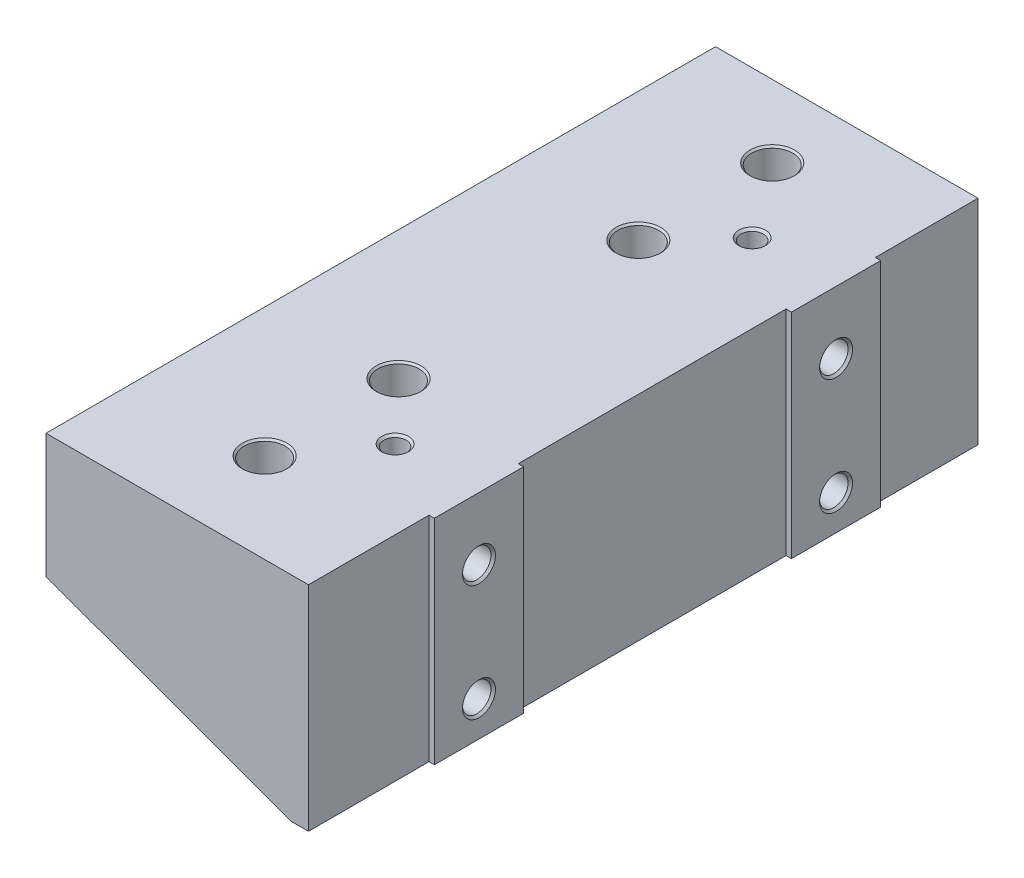
SolidWorks part; units mm, degrees
material "6061-T6 Al"
ref_plane "Front" through (0, 0, 0) normal (0, 0, 1) x (1, 0, 0)
ref_plane "Top" through (0, 0, 0) normal (0, 1, 0) x (1, 0, 0)
ref_plane "Right" through (0, 0, 0) normal (1, 0, 0) x (0, 0, -1)
sketch "Sketch13" plane through (0, 0, 0) normal (0, 0, 1) x (1, 0, 0)
  line L0 (0, -60.7572) -> (-6.35, -60.7572)
  line L8 (-76.2, -35.3339) -> (-6.35, -60.7572)
  line L9 (0, -60.7572) -> (0, 0)
  line L10 (0, 0) -> (-76.2, 0)
  line L11 (-76.2, 0) -> (-76.2, -35.3339)
  dimension "D1" = 76.2
  dimension "D2" = 6.35
  dimension "D3" = 70
  dimension "D4" = 60.7572
extrude "Extrude1" add sketch "Sketch13" along normal mid plane 190.5
hole_wizard "Tapped Hole for 3/8-16 Helicoil1" positions "Sketch15" profile "Sketch14" tap size "3/8-16" standard "Helicoil® Inch" end condition through all
sketch "Sketch15" plane through (0, 0, 0) normal (0, 1, 0) x (-1, 0, 0)
  point P0 (39.497, 69.7484)
  point P3 (39.497, 31.6484)
  point P6 (39.497, -36.576)
  point P9 (39.497, -74.676)
  dimension "D1" = 31.6484
  dimension "D2" = 38.1
  dimension "D3" = 38.1
  dimension "D4" = 74.676
  dimension "D5" = 39.497
sketch "Sketch14" plane through (-39.497, 0, 69.7484) normal (1, 0, 0) x (0, 0, 1)
  line L0 (0, 0) -> (0, 60.7572)
  line L1 (0, 60.7572) -> (5.0419, 60.7572)
  line L3 (5.0419, 60.7572) -> (5.0419, 28.702)
  line L4 (5.8445, 28.702) -> (5.0419, 28.702)
  line L5 (5.8445, 28.702) -> (5.8445, 0.5055)
  line L6 (5.8445, 0.5055) -> (6.35, 0)
  line L7 (6.35, 0) -> (0, 0)
  line L8 (-5.8445, 0.5055) -> (-6.35, 0) construction
  line L11 (0, -6.35) -> (0, 107.95) construction
  dimension "Thru Tap Drill Dia." = 10.0838
  dimension "Thru Tap Drill Depth" = 60.7572
  dimension "Thread Major Dia." = 11.6891
  dimension "Thread Depth" = 28.702
  dimension "Near C'Sink Dia." = 12.7
  dimension "Near C'Sink Angle" = 90
hole_wizard "Tapped Hole for 1/4-20 Helicoil1" positions "Sketch17" profile "Sketch16" tap size "1/4-20" standard "Helicoil® Inch"
sketch "Sketch17" plane through (0, 0, 0) normal (1, 0, 0) x (0, 0, -1)
  point P0 (-48.26, -17.78)
  point P29 (-48.26, -50.8)
  point P31 (53.34, -50.8)
  point P64 (53.34, -17.78)
  dimension "D1" = 101.6
  dimension "D2" = 33.02
  dimension "D3" = 48.26
  dimension "D4" = 17.78
sketch "Sketch16" plane through (0, -17.78, 48.26) normal (0, 1, 0) x (0, 0, -1)
  line L0 (0, 0) -> (0, 25.9058)
  line L1 (0, 25.9058) -> (3.3782, 23.876)
  line L2 (3.3782, 23.876) -> (3.3782, 15.748)
  line L3 (3.3782, 15.748) -> (4.0475, 15.748)
  line L5 (4.0475, 15.748) -> (4.0475, 0.635)
  line L6 (4.0475, 0.635) -> (4.6825, 0)
  line L7 (4.6825, 0) -> (0, 0)
  line L8 (-4.0475, 0.635) -> (-4.6825, 0) construction
  line L10 (0, 25.9058) -> (-3.3782, 23.876) construction
  line L11 (0, -6.35) -> (0, 107.95) construction
  dimension "Tap Drill Dia." = 6.7564
  dimension "Tap Drill Depth" = 23.876
  dimension "Thread Major Dia." = 8.095
  dimension "Thread Depth" = 15.748
  dimension "Near C'Sink Dia." = 9.365
  dimension "Near C'Sink Angle" = 90
  dimension "Drill Angle" = 118
hole_wizard "1/4 (0.25) Diameter Hole1" positions "Sketch19" profile "Sketch18" hole size "1/4" standard "Ansi Inch" end condition through all
sketch "Sketch19" plane through (0, 0, 0) normal (0, 1, 0) x (-1, 0, 0)
  line L0 (23.876, -56.7182) -> (23.876, -49.9618) construction
  line L1 (23.876, 44.8818) -> (23.876, 51.6382) construction
  point P0 (23.876, -53.34)
  point P4 (23.876, 48.26)
sketch "Sketch18" plane through (-23.876, 0, -53.34) normal (1, 0, 0) x (0, 0, 1)
  line L0 (0, 0) -> (0, 60.7572)
  line L1 (0, 60.7572) -> (3.175, 60.7572)
  line L2 (3.175, 60.7572) -> (3.175, 0.635)
  line L3 (3.175, 0.635) -> (3.81, 0)
  line L5 (3.81, 0) -> (0, 0)
  line L6 (-3.175, 0.635) -> (-3.81, 0) construction
  line L11 (0, -6.35) -> (0, 107.95) construction
  dimension "Thru Hole Dia." = 6.35
  dimension "Thru Hole Depth" = 60.7572
  dimension "Near C'Sink Dia." = 7.62
  dimension "Near C'Sink Angle" = 90
sketch "Sketch20" plane through (0, 0, 0) normal (1, 0, 0) x (0, 0, -1)
  line L0 (-95.25, 0) -> (95.25, 0) construction
  line L1 (-35.56, 0) -> (40.64, 0)
  line L2 (-35.56, 0) -> (-35.56, -60.7572)
  line L3 (-35.56, -60.7572) -> (40.64, -60.7572)
  line L4 (40.64, 0) -> (40.64, -60.7572)
  line L5 (-95.25, -60.7572) -> (95.25, -60.7572) construction
  line L7 (95.25, 0) -> (66.04, 0)
  line L8 (95.25, 0) -> (95.25, -60.7572)
  line L9 (95.25, -60.7572) -> (66.04, -60.7572)
  line L10 (66.04, 0) -> (66.04, -60.7572)
  line L11 (-95.25, 0) -> (-60.96, 0)
  line L12 (-95.25, 0) -> (-95.25, -60.7572)
  line L13 (-95.25, -60.7572) -> (-60.96, -60.7572)
  line L14 (-60.96, 0) -> (-60.96, -60.7572)
  circle A0 centre (53.34, -17.78) radius 4.6825 construction
  circle A1 centre (-48.26, -17.78) radius 4.6825 construction
  dimension "D3" = 12.7
  dimension "D1" = 25.4
  dimension "D2" = 25.4
  dimension "D4" = 12.7
extrude "Extrude2" cut sketch "Sketch20" against normal blind 1.524
